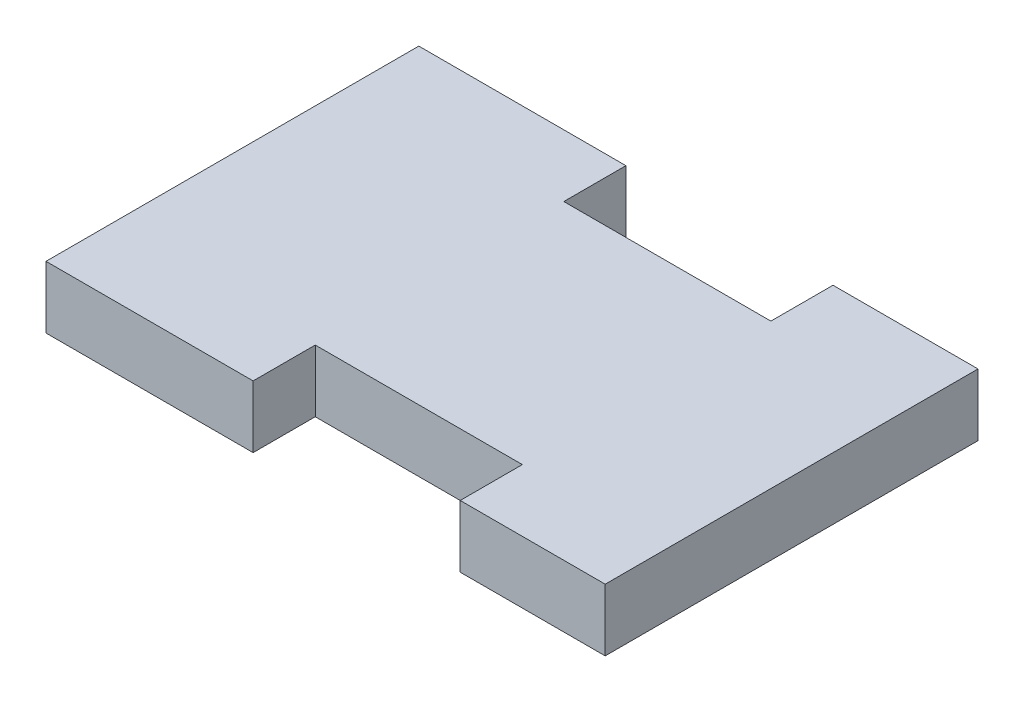
SolidWorks part; units mm, degrees
ref_plane "Front" through (0, 0, 0) normal (0, 0, 1) x (1, 0, 0)
ref_plane "Top" through (0, 0, 0) normal (0, 1, 0) x (1, 0, 0)
ref_plane "Right" through (0, 0, 0) normal (1, 0, 0) x (0, 0, -1)
sketch "Skizze1" plane through (0, 0, 0) normal (0, 1, 0) x (1, 0, 0)
  line L5 (0, 0) -> (27, 0) construction
  line L6 (0, 0) -> (0, 18) construction
  line L7 (0, 18) -> (27, 18) construction
  line L8 (27, 0) -> (27, 18) construction
  line L104 (0, 0) -> (10.0002, 0)
  line L105 (10.0002, 3) -> (10.0002, 0)
  line L106 (10.0002, 3) -> (19.9992, 3)
  line L107 (19.9992, 3) -> (19.9992, 0)
  line L108 (19.9992, 0) -> (26.9997, 0)
  line L109 (0, 18) -> (10.0002, 18)
  line L110 (10.0002, 18) -> (10.0002, 15)
  line L111 (10.0002, 15) -> (19.9992, 15)
  line L112 (19.9992, 18) -> (19.9992, 15)
  line L113 (19.9992, 18) -> (26.9997, 18)
  line L114 (0, 0) -> (0, 18)
  line L115 (26.9997, 0) -> (26.9997, 18)
  dimension "D1" = 18
  dimension "D2" = 27
extrude "Aufsatz-Linear austragen1" add sketch "Skizze1" along normal blind 3
